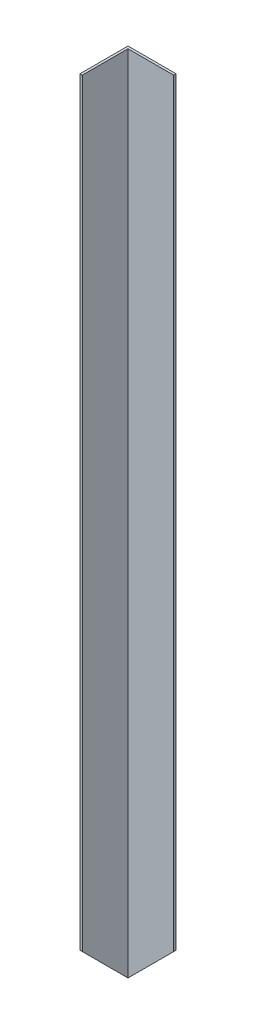
SolidWorks part; units mm, degrees
ref_plane "Plan de face" through (0, 0, 0) normal (0, 0, 1) x (1, 0, 0)
ref_plane "Plan de dessus" through (0, 0, 0) normal (0, 1, 0) x (1, 0, 0)
ref_plane "Plan de droite" through (0, 0, 0) normal (1, 0, 0) x (0, 0, -1)
sketch "Esquisse1" plane through (0, 0, 0) normal (0, 1, 0) x (1, 0, 0)
  line L1 (-20, 20.1136) -> (20, 20.1136)
  line L2 (-20, 20.1136) -> (-20, -19.8864)
  line L3 (-20, -19.8864) -> (-18, -19.8864)
  line L4 (20, 20.1136) -> (20, 18.1136)
  line L5 (-18, 18.1136) -> (20, 18.1136)
  line L6 (-18, 18.1136) -> (-18, -19.8864)
  dimension "D1" = 20
  dimension "D2" = 40
  dimension "D3" = 40
  dimension "D4" = 2
  dimension "D5" = 2
extrude "Boss.-Extru.1" add sketch "Esquisse1" along normal blind 672
sketch "Esquisse2" plane through (0, 0, -20.1136) normal (0, 0, -1) x (-1, 0, 0)
  line L0 (20, 0) -> (-20, 40)
  line L1 (20, 0) -> (-20, 0)
  line L2 (-20, 0) -> (-20, 40)
  dimension "D1" = 45
extrude "Enlèv. mat.-Extru.1" cut sketch "Esquisse2" against normal blind 590
sketch "Esquisse3" plane through (-20, 0, 0) normal (-1, 0, 0) x (0, 0, 1)
  line L0 (-20.1136, 0) -> (19.8864, 40)
  line L1 (19.8864, 672) -> (19.8864, 0) construction
  line L2 (19.8864, 40) -> (19.8864, 0)
  line L3 (19.8864, 0) -> (-20.1136, 0)
  dimension "D1" = 45
extrude "Enlèv. mat.-Extru.2" cut sketch "Esquisse3" against normal blind 590
